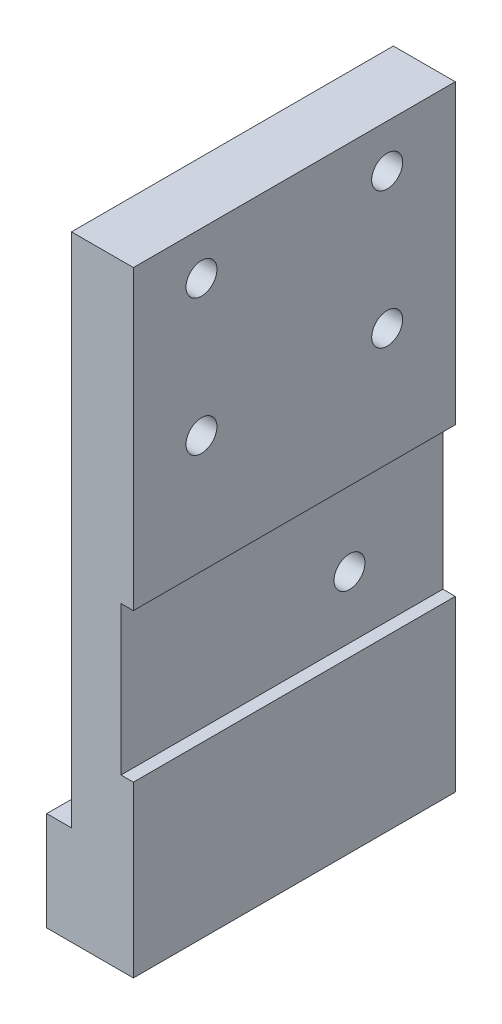
SolidWorks part; units mm, degrees
ref_plane "前视基准面" through (0, 0, 0) normal (0, 0, 1) x (1, 0, 0)
ref_plane "上视基准面" through (0, 0, 0) normal (0, 1, 0) x (1, 0, 0)
ref_plane "右视基准面" through (0, 0, 0) normal (1, 0, 0) x (0, 0, -1)
sketch "草图1" plane through (0, 0, 0) normal (0, 0, 1) x (1, 0, 0)
  line L1 (0, 0) -> (30, 0)
  line L2 (0, 0) -> (0, 6)
  line L3 (0, 6) -> (30, 6)
  line L4 (30, 0) -> (30, 6)
  dimension "D1" = 30
  dimension "D2" = 6
extrude "凸台-拉伸1" add sketch "草图1" along normal blind 5
sketch "草图2" plane through (0, 0, 5) normal (0, 0, 1) x (1, 0, 0)
  line L0 (15, 0) -> (15, 6) construction
  line L1 (0, 0) -> (30, 0) construction
  line L2 (30, 6) -> (0, 6) construction
  circle A0 centre (22.5, 3) radius 2.25
  circle A1 centre (7.5, 3) radius 2.25
  dimension "D1" = 3
  dimension "D2" = 4.5
  dimension "D3" = 15
extrude "切除-拉伸1" cut sketch "草图2" against normal through all
sketch "草图3" plane through (0, 0, 5) normal (0, 0, 1) x (1, 0, 0)
  line L1 (30, 6) -> (-10, 6)
  line L2 (30, 6) -> (30, 36)
  line L3 (30, 36) -> (-10, 36)
  line L4 (-10, 6) -> (-10, 36)
  dimension "D1" = 40
  dimension "D2" = 30
extrude "凸台-拉伸2" add sketch "草图3" against normal blind 5
sketch "草图4" plane through (0, 0, 5) normal (0, 0, 1) x (1, 0, 0)
  line L1 (30, 36) -> (27, 36)
  line L2 (30, 36) -> (30, 16)
  line L3 (30, 16) -> (27, 16)
  line L4 (27, 36) -> (27, 16)
  dimension "D1" = 3
  dimension "D2" = 20
extrude "切除-拉伸2" cut sketch "草图4" against normal blind 10
sketch "草图7" plane through (0, 6, 0) normal (0, -1, 0) x (1, 0, 0)
  line L1 (0, 0) -> (-10, 0)
  line L2 (0, 0) -> (0, 5)
  line L3 (0, 5) -> (-10, 5)
  line L4 (-10, 0) -> (-10, 5)
extrude "切除-拉伸3" cut sketch "草图7" against normal through all
sketch "草图9" plane through (0, 36, 0) normal (0, 1, 0) x (1, 0, 0)
  line L0 (27, -5) -> (0, -5) construction
  line L1 (22.4, -5) -> (17.4, -5)
  line L2 (22.4, -5) -> (22.4, 0)
  line L3 (22.4, 0) -> (17.4, 0)
  line L4 (17.4, -5) -> (17.4, 0)
  line L5 (27, 0) -> (0, 0) construction
  line L6 (27, 0) -> (27, -5) construction
  dimension "D1" = 4.6
  dimension "D2" = 5
extrude "凸台-拉伸5" add sketch "草图9" along normal blind 18
sketch "草图10" plane through (0, 0, 5) normal (0, 0, 1) x (1, 0, 0)
  line L1 (0, 36) -> (10, 36)
  line L2 (0, 36) -> (0, 16)
  line L3 (0, 16) -> (10, 16)
  line L4 (10, 36) -> (10, 16)
  dimension "D1" = 20
  dimension "D2" = 10
extrude "切除-拉伸4" cut sketch "草图10" against normal blind 18
sketch "草图11" plane through (0, 36, 0) normal (0, 1, 0) x (1, 0, 0)
  line L1 (27, -5) -> (10, -5)
  line L2 (27, -5) -> (27, 0)
  line L3 (27, 0) -> (10, 0)
  line L4 (10, -5) -> (10, 0)
extrude "凸台-拉伸6" add sketch "草图11" along normal blind 0.7
sketch "草图12" plane through (0, 54, 0) normal (0, 1, 0) x (1, 0, 0)
  line L1 (22.4, -5) -> (17.4, -5)
  line L2 (22.4, -5) -> (22.4, 0)
  line L3 (22.4, 0) -> (17.4, 0)
  line L4 (17.4, -5) -> (17.4, 0)
extrude "凸台-拉伸7" add sketch "草图12" along normal blind 0.7
sketch "草图13" plane through (17.4, 0, 0) normal (-1, 0, 0) x (0, 0, 1)
  line L0 (2.5, 54.7) -> (2.5, 36.7745) construction
  line L1 (0, 54.7) -> (5, 54.7) construction
  line L3 (15.5, 36.7) -> (-10.5, 36.7)
  line L4 (15.5, 36.7) -> (15.5, 54.7)
  line L5 (15.5, 54.7) -> (-10.5, 54.7)
  line L6 (-10.5, 36.7) -> (-10.5, 54.7)
  dimension "D1" = 26
extrude "凸台-拉伸8" add sketch "草图13" against normal blind 5
hole_wizard "M3 螺纹孔1" positions "草图14" profile "草图15" tap size "M3" standard "ISO"
sketch "草图14" plane through (22.4, 0, 0) normal (1, 0, 0) x (0, 0, -1)
  point P0 (-10, 40.2)
  point P3 (5, 40.2)
  point P6 (5, 51.2)
  point P9 (-10, 51.2)
sketch "草图15" plane through (22.4, 40.2, 10) normal (0, 1, 0) x (0, 0, -1)
  line L0 (0, 0) -> (0, 8.2511)
  line L1 (0, 8.2511) -> (1.25, 7.5)
  line L2 (1.25, 7.5) -> (1.25, 0)
  line L5 (1.25, 0) -> (0, 0)
  line L10 (0, 8.2511) -> (-1.25, 7.5) construction
  line L11 (0, -6.35) -> (0, 107.95) construction
  dimension "螺纹孔钻头直径" = 2.5
  dimension "螺纹孔钻头深度" = 7.5
  dimension "导头角度" = 118
cosmetic thread "孔螺蚊线5" parameters "D1"=5, "D2"=3
cosmetic thread "孔螺蚊线6" parameters "D1"=5, "D2"=3
cosmetic thread "孔螺蚊线7" parameters "D1"=5, "D2"=3
cosmetic thread "孔螺蚊线8" parameters "D1"=5, "D2"=3
sketch "草图16" plane through (30, 0, 0) normal (1, 0, 0) x (0, 0, -1)
  line L1 (0, 36.7) -> (-14.2671, 36.7)
  line L2 (0, 36.7) -> (0, -2.5993)
  line L3 (0, -2.5993) -> (-14.2671, -2.5993)
  line L4 (-14.2671, 36.7) -> (-14.2671, -2.5993)
extrude "切除-拉伸5" cut sketch "草图16" against normal through all
sketch "草图17" plane through (0, 36.7, 0) normal (0, -1, 0) x (1, 0, 0)
  line L1 (17.4, 15.5) -> (22.4, 15.5)
  line L2 (17.4, 15.5) -> (17.4, -10.5)
  line L3 (17.4, -10.5) -> (22.4, -10.5)
  line L4 (22.4, 15.5) -> (22.4, -10.5)
extrude "凸台-拉伸9" add sketch "草图17" along normal blind 30.7
sketch "草图18" plane through (0, 6, 0) normal (0, -1, 0) x (1, 0, 0)
  line L1 (22.4, 15.5) -> (17.4, 15.5)
  line L2 (22.4, 15.5) -> (22.4, -10.5)
  line L3 (22.4, -10.5) -> (17.4, -10.5)
  line L4 (17.4, 15.5) -> (17.4, -10.5)
extrude "凸台-拉伸10" add sketch "草图18" along normal blind 1
sketch "草图20" plane through (17.4, 0, 0) normal (-1, 0, 0) x (0, 0, 1)
  line L0 (-10.5, 54.7) -> (-10.5, 5) construction
  line L1 (15.5, 5) -> (-10.5, 5)
  line L2 (15.5, 5) -> (15.5, 13)
  line L3 (15.5, 13) -> (-10.5, 13)
  line L4 (-10.5, 5) -> (-10.5, 13)
  dimension "D1" = 8
extrude "凸台-拉伸11" add sketch "草图20" along normal blind 2
hole_wizard "M4 螺纹孔1" positions "草图21" profile "草图22" tap size "M4" standard "ISO"
sketch "草图21" plane through (0, 5, 0) normal (0, -1, 0) x (-1, 0, 0)
  point P0 (-18.9, -7.6405)
  point P3 (-18.9, 3.3595)
sketch "草图22" plane through (18.9, 5, 7.6405) normal (1, 0, 0) x (0, 0, -1)
  line L0 (0, 0) -> (0, 6.9914)
  line L1 (0, 6.9914) -> (1.65, 6)
  line L2 (1.65, 6) -> (1.65, 0)
  line L5 (1.65, 0) -> (0, 0)
  line L10 (0, 6.9914) -> (-1.65, 6) construction
  line L11 (0, -6.35) -> (0, 107.95) construction
  dimension "螺纹孔钻头直径" = 3.3
  dimension "螺纹孔钻头深度" = 6
  dimension "导头角度" = 118
cosmetic thread "孔螺蚊线9" parameters "D1"=6, "D2"=4
cosmetic thread "孔螺蚊线10" parameters "D1"=6, "D2"=4
sketch "草图23" plane through (22.4, 0, 0) normal (1, 0, 0) x (0, 0, -1)
  line L0 (10.5, 54.7) -> (10.5, 5) construction
  line L1 (10.5, 18.7) -> (-15.5, 18.7)
  line L2 (10.5, 18.7) -> (10.5, 30.7)
  line L3 (10.5, 30.7) -> (-15.5, 30.7)
  line L4 (-15.5, 18.7) -> (-15.5, 30.7)
  line L5 (-15.5, 5) -> (-15.5, 54.7) construction
  line L6 (-15.5, 54.7) -> (10.5, 54.7) construction
  dimension "D1" = 12
  dimension "D2" = 24
extrude "切除-拉伸6" cut sketch "草图23" against normal blind 1
hole_wizard "M3 螺纹孔2" positions "草图24" profile "草图25" tap size "M3" standard "ISO"
sketch "草图24" plane through (21.4, 0, 0) normal (1, 0, 0) x (0, 0, -1)
  point P0 (2.9557, 23.7)
sketch "草图25" plane through (21.4, 23.7, -2.9557) normal (0, 1, 0) x (0, 0, -1)
  line L0 (0, 0) -> (0, 8.2511)
  line L1 (0, 8.2511) -> (1.25, 7.5)
  line L2 (1.25, 7.5) -> (1.25, 0)
  line L5 (1.25, 0) -> (0, 0)
  line L10 (0, 8.2511) -> (-1.25, 7.5) construction
  line L11 (0, -6.35) -> (0, 107.95) construction
  dimension "螺纹孔钻头直径" = 2.5
  dimension "螺纹孔钻头深度" = 7.5
  dimension "导头角度" = 118
cosmetic thread "孔螺蚊线11" parameters "D1"=4, "D2"=3
